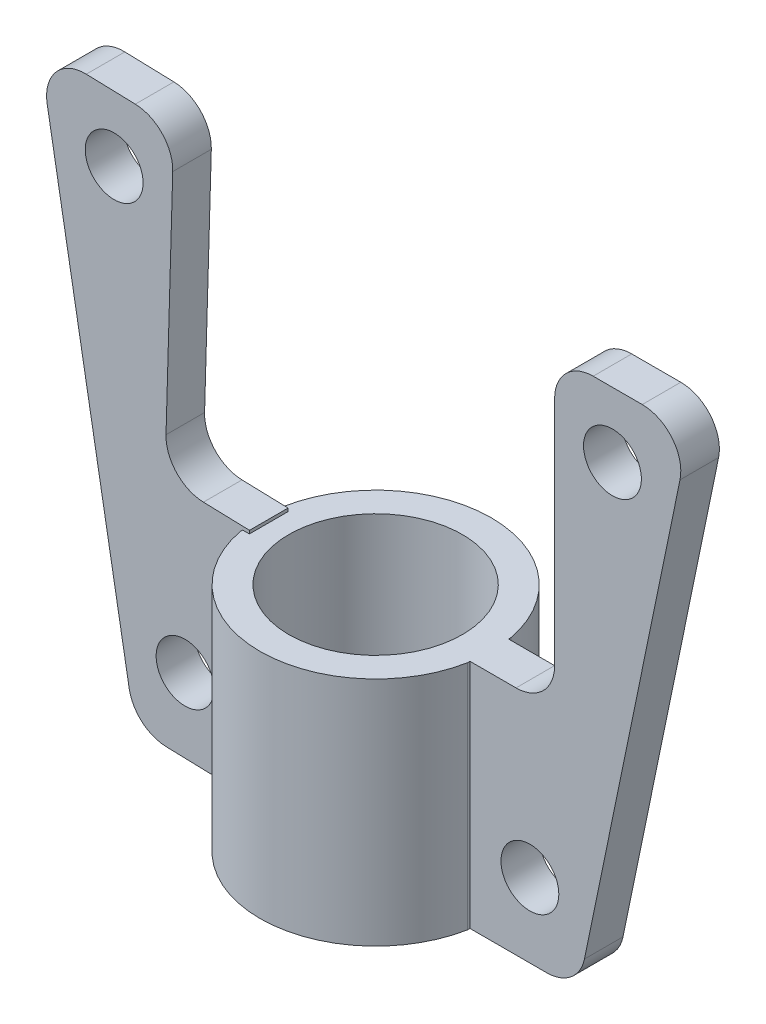
SolidWorks part; units mm, degrees
ref_plane "Alzado" through (0, 0, 0) normal (0, 0, 1) x (1, 0, 0)
ref_plane "Planta" through (0, 0, 0) normal (0, 1, 0) x (1, 0, 0)
ref_plane "Vista lateral" through (0, 0, 0) normal (1, 0, 0) x (0, 0, -1)
sketch "Croquis1" plane through (0, 0, 0) normal (0, 1, 0) x (1, 0, 0)
  line L2 (-29.4646, 5.6424) -> (-29.4646, -5.6424)
  line L4 (29.4646, 5.6424) -> (29.4646, -5.6424)
  circle A0 centre (0, 0) radius 22.5
  arc A1 (-29.4646, -5.6424) -> (29.4646, -5.6424) centre (0, 0) ccw
  arc A2 (29.4646, 5.6424) -> (-29.4646, 5.6424) centre (0, 0) ccw
extrude "Saliente-Extruir1" add sketch "Croquis1" along normal blind 60
sketch "Croquis2" plane through (0, 0, 0) normal (0, 0, 1) x (1, 0, 0)
  line L0 (0, 0) -> (11.4118, 784.2708) construction
  line L1 (29.4646, 60) -> (29.4646, 0) construction
  line L2 (29.4646, 60) -> (29.4646, 0)
  line L3 (29.4646, 0) -> (49.3599, 0)
  line L4 (59.1533, 7.978) -> (83.9296, 127.978)
  line L5 (74.1362, 140) -> (61.4118, 140)
  line L6 (51.4118, 130) -> (51.4118, 70)
  line L7 (41.4118, 60) -> (29.4646, 60)
  line L9 (-39.6486, 61.1795) -> (-27.7064, 60.8319)
  line L10 (-47.6076, 131.4408) -> (-49.3534, 71.4662)
  line L11 (-70.0314, 142.0978) -> (-57.3124, 141.7275)
  line L12 (-58.8961, 9.6957) -> (-80.1705, 130.3658)
  line L13 (-29.4521, 0.8573) -> (-49.339, 1.4362)
  line L14 (-27.7064, 60.8319) -> (-29.4521, 0.8573)
  arc A0 (41.4118, 60) -> (51.4118, 70) centre (41.4118, 70) ccw
  arc A1 (59.1533, 7.978) -> (49.3599, 0) centre (49.3599, 10) cw
  arc A2 (83.9296, 127.978) -> (74.1362, 140) centre (74.1362, 130) ccw
  arc A3 (51.4118, 130) -> (61.4118, 140) centre (61.4118, 130) cw
  circle A4 centre (-62.8005, 125.0319) radius 7.5
  circle A5 centre (45, 19.2036) radius 7.5
  circle A6 centre (-44.4222, 20.5047) radius 7.5
  circle A7 centre (66.4118, 123.1518) radius 7.5
  arc A8 (-47.6076, 131.4408) -> (-57.3124, 141.7275) centre (-57.6034, 131.7318) ccw
  arc A9 (-80.1705, 130.3658) -> (-70.0314, 142.0978) centre (-70.3224, 132.102) cw
  arc A10 (-58.8961, 9.6957) -> (-49.339, 1.4362) centre (-49.048, 11.4319) ccw
  arc A11 (-39.6486, 61.1795) -> (-49.3534, 71.4662) centre (-39.3576, 71.1753) cw
  point P13 (57.5061, 0)
  point P16 (86.4118, 140)
  point P19 (51.4118, 140)
  point P24 (67.774, 140)
  point P25 (39.4122, 0)
  point P29 (0, 0)
  point P48 (-47.3167, 141.4366)
  point P49 (-82.3019, 142.4549)
  point P50 (-57.4817, 1.6732)
  dimension "D6" = 10
  dimension "D7" = 15
  dimension "D8" = 15
  dimension "D1" = 40
  dimension "D2" = 57.5
  dimension "D3" = 140
  dimension "D4" = 11.666
  dimension "D5" = 35
  dimension "D9" = 65.7299
  dimension "D10" = 15
  dimension "D11" = 45
  dimension "D12" = 20
extrude "Saliente-Extruir2" add sketch "Croquis2" along normal mid plane 10
